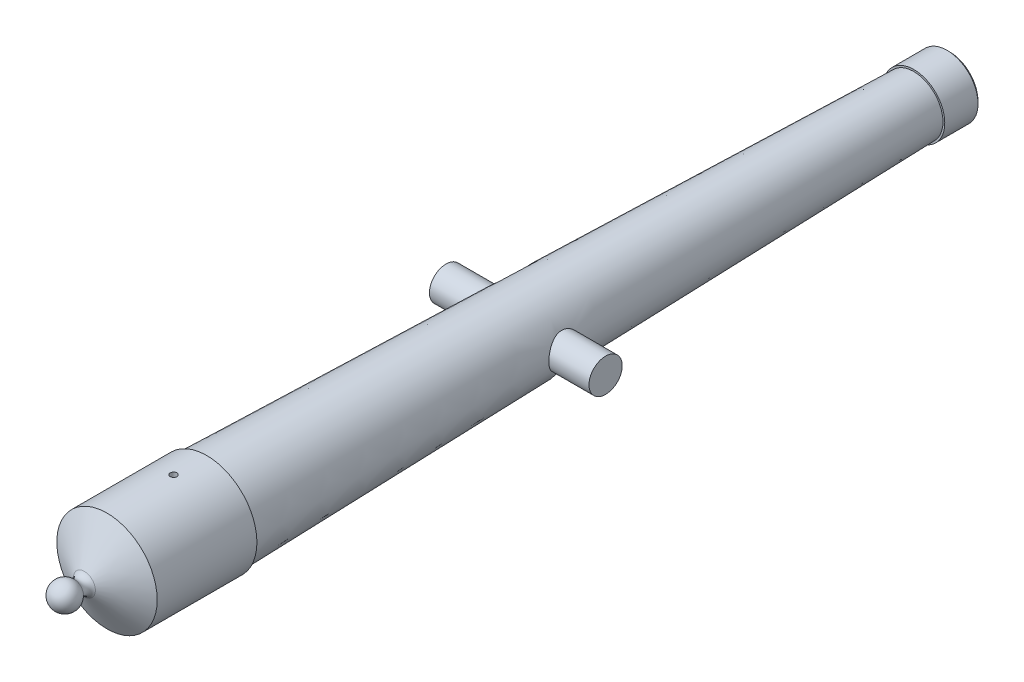
SolidWorks part; units mm, degrees
material "Malleable Cast Iron"
ref_plane "Front Plane" through (0, 0, 0) normal (0, 0, 1) x (1, 0, 0)
ref_plane "Top Plane" through (0, 0, 0) normal (0, 1, 0) x (1, 0, 0)
ref_plane "Right Plane" through (0, 0, 0) normal (1, 0, 0) x (0, 0, -1)
sketch "Sketch1" plane through (0, 0, 0) normal (1, 0, 0) x (0, 0, -1)
  line L0 (-101.6, 0) -> (101.6, 0) construction
  line L1 (-76.2, 2.8321) -> (76.2, 2.8321)
  line L2 (81.0017, 3.6788) -> (81.0017, 5.3721)
  line L5 (-76.2, 2.8321) -> (-76.2, 0)
  line L6 (-76.2, 0) -> (-85.5458, 0)
  line L7 (-90.6258, 0) -> (-85.5458, 0)
  line L16 (81.0017, 3.6788) -> (76.2, 2.8321)
  line L17 (-80.01, 9.5883) -> (-60.96, 9.5883)
  line L18 (-60.96, 9.0895) -> (74.1437, 5.5517)
  line L19 (-60.96, 9.5883) -> (-60.96, 9.0895)
  line L20 (-80.01, 9.5883) -> (-84.3334, 2.1)
  line L21 (80.4937, 5.3854) -> (80.4937, 5.8934)
  line L22 (80.4937, 5.8934) -> (74.1437, 5.8934)
  line L23 (74.1437, 5.8934) -> (74.1437, 5.5517)
  line L24 (80.4937, 5.3854) -> (81.0017, 5.3721)
  arc A18 (-86.3175, 1.8233) -> (-90.6258, 0) centre (-88.0858, 0) ccw
  arc A19 (-84.3334, 2.1) -> (-86.3175, 1.8233) centre (-85.4333, 2.735) cw
  point P5 (0, 2.8321)
  point P14 (81.0017, 4.5254)
  dimension "D11" = 5.08
  dimension "D12" = 1.27
  dimension "D1" = 203.2
  dimension "D3" = 2.8321
  dimension "D8" = 10
  dimension "D2" = 2.54
  dimension "D4" = 1.6933
  dimension "D5" = 157.2017
  dimension "D6" = 1.5
  dimension "D7" = 19.05
  dimension "D9" = 3.81
  dimension "D10" = 60
  dimension "D13" = 0.508
  dimension "D14" = 0.508
  dimension "D15" = 6.35
revolve "Revolve1" add sketch "Sketch1" angle 360 about L0
sketch "Sketch3" plane through (0, 0, 0) normal (1, 0, 0) x (0, 0, -1)
  circle A3 centre (0, 0) radius 3.175
  dimension "D1" = 6.35
extrude "Boss-Extrude1" add sketch "Sketch3" along normal mid plane 10.16 from offset 10.16
mirror "Mirror1" about plane through (0, 0, 0) normal (1, 0, 0) of "Boss-Extrude1"
sketch "Sketch4" plane through (0, 0, 0) normal (0, 1, 0) x (1, 0, 0)
  line L0 (9.5883, -60.96) -> (-9.5883, -60.96) construction
  circle A0 centre (0, -67.31) radius 0.635
  dimension "D1" = 1.27
  dimension "D2" = 6.35
extrude "Cut-Extrude1" cut sketch "Sketch4" along normal through all
equation "\"D4@Sketch1\"=\"D2@Sketch1\"*2/3"
